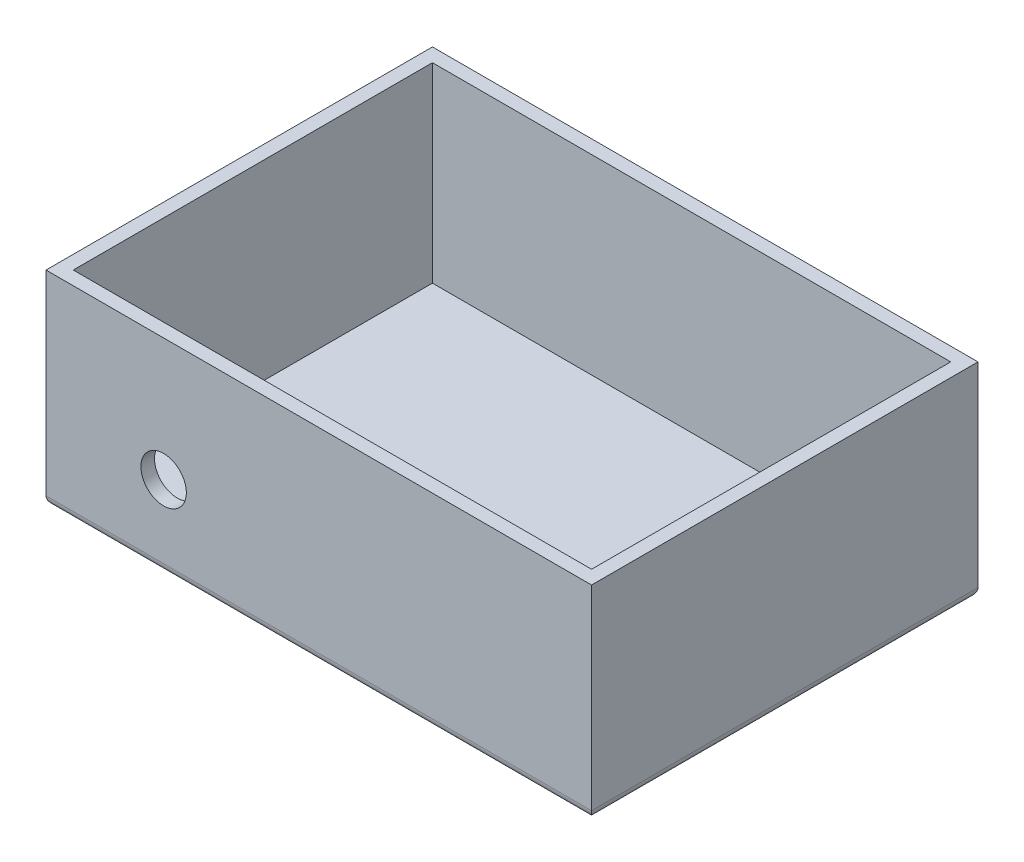
SolidWorks part; units mm, degrees
ref_plane "Front Plane" through (0, 0, 0) normal (0, 0, 1) x (1, 0, 0)
ref_plane "Top Plane" through (0, 0, 0) normal (0, 1, 0) x (1, 0, 0)
ref_plane "Right Plane" through (0, 0, 0) normal (1, 0, 0) x (0, 0, -1)
sketch "Sketch1" plane through (0, 0, 0) normal (0, 1, 0) x (1, 0, 0)
  line L1 (60, -42.5) -> (-60, -42.5)
  line L2 (60, -42.5) -> (60, 42.5)
  line L3 (60, 42.5) -> (-60, 42.5)
  line L4 (-60, -42.5) -> (-60, 42.5)
  line L5 (60, -42.5) -> (-60, 42.5) construction
  line L6 (60, 42.5) -> (-60, -42.5) construction
  point P0 (0, 0)
  dimension "D1" = 120
  dimension "D2" = 85
extrude "Boss-Extrude1" add sketch "Sketch1" along normal blind 45
shell "Shell1" thickness 3
sketch "Sketch5" plane through (0, 0, 39.5) normal (0, 0, -1) x (-1, 0, 0)
  line L0 (57, 3) -> (-57, 3) construction
  circle A0 centre (34.1303, 18) radius 5
  point P2 (0, 0)
  dimension "D1" = 10
  dimension "D2" = 15
extrude "Cut-Extrude2" cut sketch "Sketch5" against normal blind 45
fillet "Fillet1" radius 2 4 edges at (0, 0, 42.5) (60, 0, 0) (0, 0, -42.5) (-60, 0, 0)
